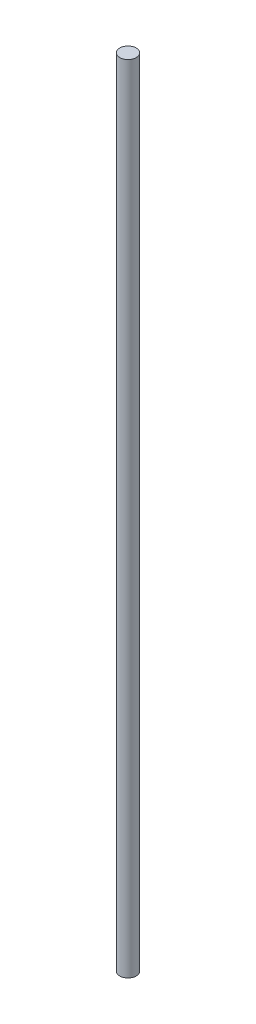
SolidWorks part; units mm, degrees
ref_plane "Front Plane" through (0, 0, 0) normal (0, 0, 1) x (1, 0, 0)
ref_plane "Top Plane" through (0, 0, 0) normal (0, 1, 0) x (1, 0, 0)
ref_plane "Right Plane" through (0, 0, 0) normal (1, 0, 0) x (0, 0, -1)
sketch "Sketch1" plane through (0, 0, 0) normal (0, 1, 0) x (1, 0, 0)
  circle A0 centre (0, 0) radius 2.3813
  dimension "D1" = 4.7625
extrude "Boss-Extrude1" add sketch "Sketch1" along normal blind 228.6
